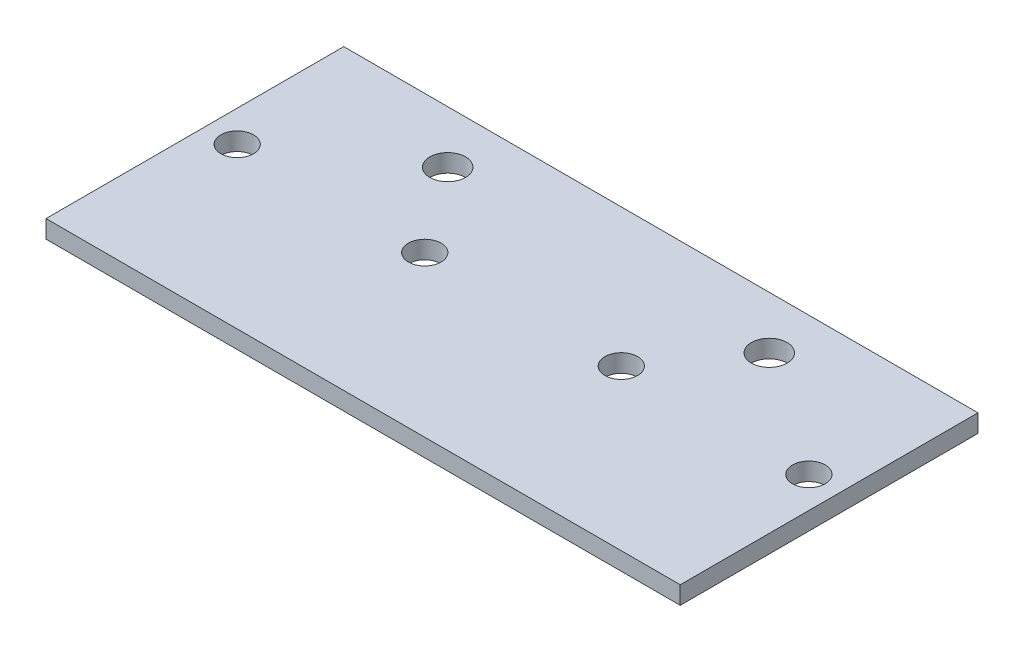
SolidWorks part; units mm, degrees
ref_plane "Front Plane" through (0, 0, 0) normal (0, 0, 1) x (1, 0, 0)
ref_plane "Top Plane" through (0, 0, 0) normal (0, 1, 0) x (1, 0, 0)
ref_plane "Right Plane" through (0, 0, 0) normal (1, 0, 0) x (0, 0, -1)
sketch "Sketch1" plane through (0, 0, 0) normal (0, 1, 0) x (1, 0, 0)
  line L1 (-53.25, -25) -> (53.25, -25)
  line L2 (-53.25, -25) -> (-53.25, 25)
  line L3 (-53.25, 25) -> (53.25, 25)
  line L4 (53.25, -25) -> (53.25, 25)
  line L5 (-53.25, -25) -> (53.25, 25) construction
  line L6 (-53.25, 25) -> (53.25, -25) construction
  point P0 (0, 0)
  dimension "D1" = 106.5
  dimension "D2" = 50
extrude "Boss-Extrude1" add sketch "Sketch1" along normal blind 3
sketch "Sketch2" plane through (0, 3, 0) normal (0, 1, 0) x (1, 0, 0)
  circle A0 centre (48, 1.85) radius 2.75
  circle A1 centre (16.5, 1.85) radius 2.75
  circle A2 centre (-16.5, 1.85) radius 2.75
  circle A3 centre (-48, 1.85) radius 2.75
  circle A4 centre (27, 16.2) radius 3
  circle A5 centre (-27, 16.2) radius 3
extrude "Cut-Extrude1" cut sketch "Sketch2" against normal through all
